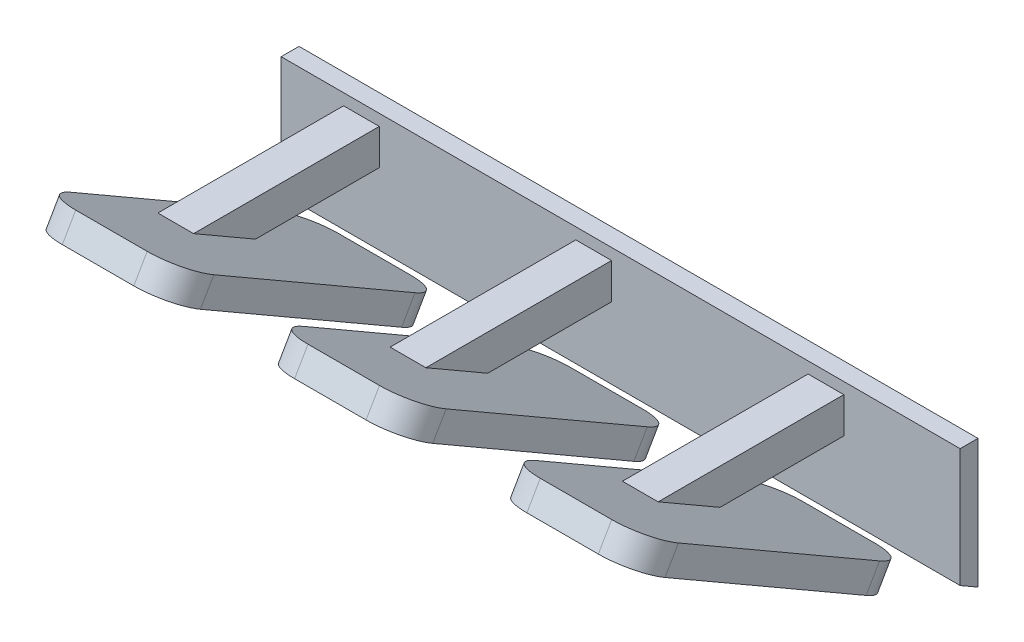
SolidWorks part; units mm, degrees
ref_plane "Front Plane" through (0, 0, 0) normal (0, 0, 1) x (1, 0, 0)
ref_plane "Top Plane" through (0, 0, 0) normal (0, 1, 0) x (1, 0, 0)
ref_plane "Right Plane" through (0, 0, 0) normal (1, 0, 0) x (0, 0, -1)
sketch "Sketch1" plane through (0, 0, 0) normal (0, 0, 1) x (1, 0, 0)
  line L1 (-25, 15) -> (25, 15)
  line L2 (-25, 15) -> (-25, -15)
  line L3 (-25, -15) -> (25, -15)
  line L4 (25, 15) -> (25, -15)
  line L5 (-25, 15) -> (25, -15) construction
  line L6 (-25, -15) -> (25, 15) construction
  point P0 (0, 0)
  dimension "D1" = 30
  dimension "D2" = 50
extrude "Boss-Extrude1" add sketch "Sketch1" along normal blind 1
sketch "Sketch2" plane through (25, 0, 0) normal (1, 0, 0) x (0, 0, -1)
  line L0 (-1, -10.9931) -> (-18.5479, -0.8618)
  line L1 (-1, -15) -> (-1, 15) construction
  line L2 (-1, -9.2611) -> (-17.7979, 0.4372)
  line L4 (-18.5479, -0.8618) -> (-17.7979, 0.4372)
  line L5 (-1, -10.9931) -> (-1, -9.2611)
  line L7 (-0.25, -9.6941) -> (-17.7979, 0.4372) construction
  dimension "D1" = 120
  dimension "D2" = 1.5
extrude "Boss-Extrude2" add sketch "Sketch2" against normal through all
sketch "Sketch3" plane through (0, -8.6778, 5.0102) normal (0, -0.866, 0.5) x (1, 0, 0)
  line L0 (25, 15.632) -> (25, -4.6305) construction
  line L1 (15, 14.132) -> (23, 14.132)
  line L2 (15, 14.132) -> (15, -2.868)
  line L3 (15, -2.868) -> (23, -2.868)
  line L4 (23, 14.132) -> (23, -2.868)
  line L5 (2, 14.132) -> (10, 14.132)
  line L6 (2, 14.132) -> (2, -2.868)
  line L7 (2, -2.868) -> (10, -2.868)
  line L8 (10, 14.132) -> (10, -2.868)
  line L9 (-11, 14.132) -> (-3, 14.132)
  line L10 (-11, 14.132) -> (-11, -2.868)
  line L11 (-11, -2.868) -> (-3, -2.868)
  line L12 (-3, 14.132) -> (-3, -2.868)
  line L13 (-25, 15.632) -> (25, 15.632) construction
  line L14 (-25, -4.6305) -> (25, -4.6305) construction
  line L15 (-25, 15.632) -> (-25, -4.6305) construction
  line L16 (-25, -4.6305) -> (25, -4.6305)
  line L17 (25, 15.632) -> (25, -4.6305)
  line L18 (-25, 15.632) -> (-25, -4.6305)
  line L19 (-25, 15.632) -> (25, 15.632)
  dimension "D1" = 8
  dimension "D2" = 17
  dimension "D3" = 5
  dimension "D4" = 2
  dimension "D5" = 5
  dimension "D6" = 1.5
  dimension "D7" = 8
  dimension "D8" = 1.5
  dimension "D9" = 17
  dimension "D10" = 8
  dimension "D11" = 17
extrude "Cut-Extrude1" cut sketch "Sketch3" against normal up to surface (1.5 mm away) up to face at (0, -4.4119, 9.3989)
sketch "Sketch4" plane through (0, 0, 1) normal (0, 0, 1) x (1, 0, 0)
  line L0 (-25, -9.2611) -> (25, -9.2611) construction
  line L1 (18.4909, -5.2611) -> (16.4909, -5.2611)
  line L2 (18.4909, -5.2611) -> (18.4909, -3.2611)
  line L3 (18.4909, -3.2611) -> (16.4909, -3.2611)
  line L4 (16.4909, -5.2611) -> (16.4909, -3.2611)
  line L5 (5.4909, -5.2611) -> (3.4909, -5.2611)
  line L6 (5.4909, -5.2611) -> (5.4909, -3.2611)
  line L7 (5.4909, -3.2611) -> (3.4909, -3.2611)
  line L8 (3.4909, -5.2611) -> (3.4909, -3.2611)
  line L9 (-7.5091, -5.2611) -> (-9.5091, -5.2611)
  line L10 (-7.5091, -5.2611) -> (-7.5091, -3.2611)
  line L11 (-7.5091, -3.2611) -> (-9.5091, -3.2611)
  line L12 (-9.5091, -5.2611) -> (-9.5091, -3.2611)
  point P14 (-8.5091, -5.2611)
  dimension "D1" = 2
  dimension "D2" = 2
  dimension "D3" = 2
  dimension "D4" = 2
  dimension "D5" = 2
  dimension "D6" = 2
  dimension "D7" = 2
  dimension "D8" = 4
  dimension "D9" = 4
  dimension "D10" = 4
  dimension "D11" = 11
  dimension "D12" = 11
extrude "Boss-Extrude3" add sketch "Sketch4" along normal up to surface (9.9282 mm away)
sketch "Sketch5" plane through (-25, 0, 0) normal (-1, 0, 0) x (0, 0, 1)
  line L0 (0.2506, -9.6951) -> (0, -9.8402)
  line L3 (0, 15) -> (0, -15) construction
  line L4 (0.25, -9.6941) -> (1, -10.9931) construction
  line L5 (0.2506, -9.6951) -> (1, -10.9931)
  line L6 (1, -10.9931) -> (1, -15) construction
  line L7 (1, -10.9931) -> (1, -15)
  line L8 (0, -9.8402) -> (0, -15)
  line L9 (1, -15) -> (0, -15) construction
  line L10 (1, -15) -> (0, -15)
extrude "Cut-Extrude2" cut sketch "Sketch5" against normal up to surface (50 mm away) up to face at (25, -4.2783, 0.6071)
sketch "Sketch6" plane through (0, 0, 1) normal (0, 0, 1) x (1, 0, 0)
  line L0 (-11, -1.6118) -> (-11, -10.1118) construction
  line L1 (-25, 15) -> (-13, 15)
  line L2 (-25, 15) -> (-25, -10.7373)
  line L3 (-25, -10.7373) -> (-13, -10.7373)
  line L4 (-13, 15) -> (-13, -10.7373)
  dimension "D1" = 2
extrude "Cut-Extrude3" cut sketch "Sketch6" against normal up to surface (1 mm away) up to face at (0, 2.5799, 0)
sketch "Sketch7" plane through (0, 0, 1) normal (0, 0, 1) x (1, 0, 0)
  line L0 (25, -9.2611) -> (25, 15) construction
  line L1 (-13, 15) -> (25, 15)
  line L2 (-13, 15) -> (-13, -2.6256)
  line L3 (-13, -2.6256) -> (25, -2.6256)
  line L4 (25, 15) -> (25, -2.6256)
extrude "Cut-Extrude4" cut sketch "Sketch7" against normal up to surface (1 mm away) up to face at (6, 2.5799, 0)
fillet "Fillet1" radius 2 4 edges at (-11, -9.4623, 2.1514) (-3, -9.4623, 2.1514) (-3, -0.9623, 16.8738) (-11, -0.9623, 16.8738)
fillet "Fillet2" radius 2 8 edges at (15, -9.4623, 2.1514) (23, -9.4623, 2.1514) (10, -9.4623, 2.1514) (2, -9.4623, 2.1514) (15, -0.9623, 16.8738) (2, -0.9623, 16.8738) (23, -0.9623, 16.8738) (10, -0.9623, 16.8738)
